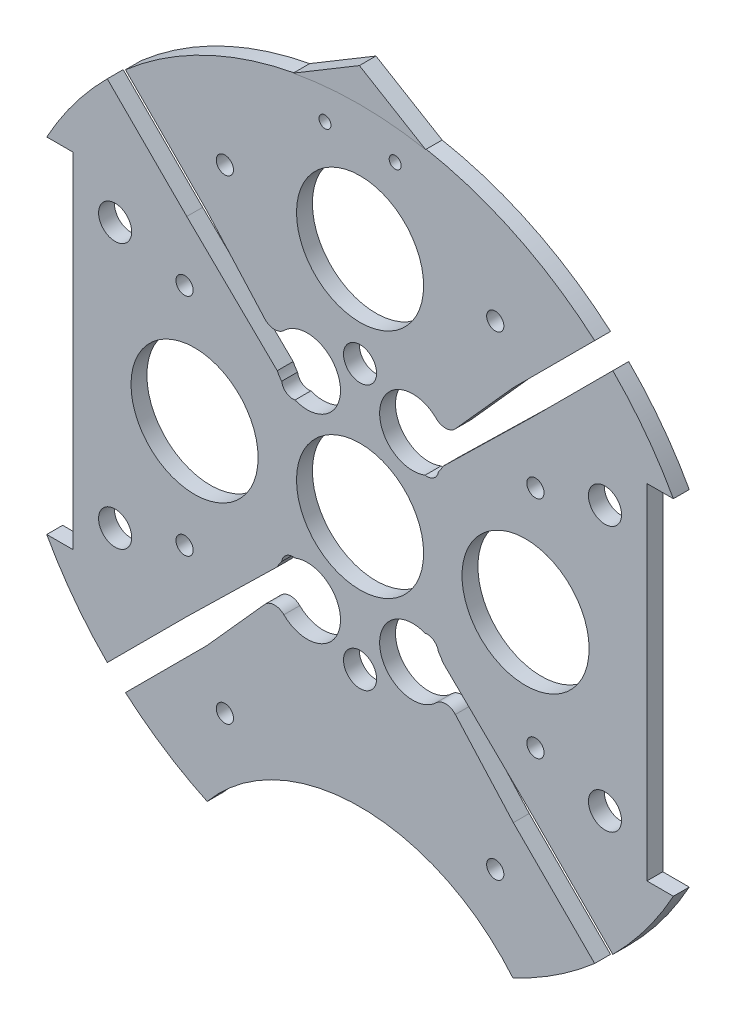
SolidWorks part; units mm, degrees
ref_plane "Front Plane" through (0, 0, 0) normal (0, 0, 1) x (1, 0, 0)
ref_plane "Top Plane" through (0, 0, 0) normal (0, 1, 0) x (1, 0, 0)
ref_plane "Right Plane" through (0, 0, 0) normal (1, 0, 0) x (0, 0, -1)
sketch "Sketch1" plane through (0, 0, 0) normal (0, 0, 1) x (1, 0, 0)
  line L0 (0, 0) -> (-82.1241, 0) construction
  line L1 (0, 0) -> (0, 95.6219) construction
  line L3 (-60.1074, 33.02) -> (-55.0274, 33.02)
  line L5 (-60.1074, -33.02) -> (-55.0274, -33.02)
  line L6 (-55.0274, 33.02) -> (-55.0274, -33.02)
  line L7 (60.1074, -33.02) -> (55.0274, -33.02)
  line L8 (60.1074, 33.02) -> (55.0274, 33.02)
  line L9 (55.0274, 33.02) -> (55.0274, -33.02)
  arc A0 (-60.1074, -33.02) -> (60.1074, -33.02) centre (0, 0) ccw
  circle A1 centre (-46.482, 10.795) radius 1.651 construction
  circle A2 centre (-21.082, 10.795) radius 1.651 construction
  circle A3 centre (-21.082, -10.795) radius 1.651 construction
  circle A4 centre (-46.482, -10.795) radius 1.651 construction
  circle A5 centre (46.482, -10.795) radius 1.651 construction
  circle A6 centre (21.082, -10.795) radius 1.651 construction
  circle A7 centre (21.082, 10.795) radius 1.651 construction
  circle A8 centre (46.482, 10.795) radius 1.651 construction
  arc A9 (60.1074, 33.02) -> (-60.1074, 33.02) centre (0, 0) ccw
  dimension "D2" = 3.302
  dimension "D3" = 3.302
  dimension "D4" = 25.4
  dimension "D5" = 10.795
  dimension "D10" = 46.482
  dimension "D12" = 10.795
  dimension "D6" = 66.04
  dimension "D7" = 5.08
  dimension "D8" = 68.58
  dimension "D9" = 68.58
  dimension "D11" = 33.02
extrude "Boss-Extrude2" add sketch "Sketch1" along normal blind 3.048
sketch "Sketch4" plane through (0, 0, 0) normal (0, 0, -1) x (-1, 0, 0)
  line L0 (0, 0) -> (0, -122.8047) construction
  line L1 (33.02, -67.2621) -> (-33.02, -67.2621)
  arc A0 (-60.1074, -33.02) -> (60.1074, -33.02) centre (0, 0) ccw construction
  circle A1 centre (0, -86.3121) radius 38.1
  dimension "D4" = 76.2
  dimension "D5" = 0
  dimension "D6" = 19.05
  dimension "D1" = 74.93
  dimension "D2" = 74.93
  dimension "D3" = 66.04
extrude "Cut-Extrude3" cut sketch "Sketch4" against normal through all
sketch "Sketch9" plane through (0, 0, 0) normal (0, 0, -1) x (-1, 0, 0)
  line L0 (12.7, 67.3938) -> (0, 75)
  line L1 (0, 75) -> (-12.7, 67.3938)
  arc A2 (12.7, 67.3938) -> (-12.7, 67.3938) centre (0, 0) ccw
extrude "Boss-Extrude3" add sketch "Sketch9" against normal blind 3.175
extrude "Cut-Extrude7" cut sketch "Sketch10" against normal through all
sketch "Sketch10" plane through (-31.3134, 132.559, 6.35) normal (0, 0, 1) x (0, 1, 0)
  line L0 (-132.559, -31.3134) -> (-245.9178, -31.3134) construction
  line L1 (-132.559, -31.3134) -> (-132.559, -129.4011) construction
  circle A0 centre (-180.819, -4.6434) radius 1.651
  circle A3 centre (-180.819, -57.9834) radius 1.651
  circle A4 centre (-84.299, -57.9834) radius 1.651
  circle A5 centre (-84.299, -4.6434) radius 1.651
extrude "Cut-Extrude8" cut sketch "Sketch11" against normal through all both and the other way through all
sketch "Sketch11" plane through (-31.3134, 132.614, 38.1) normal (0, 0, 1) x (0, 1, 0)
  line L0 (-132.614, -31.3134) -> (-132.614, 57.8454) construction
  line L1 (-132.614, -31.3134) -> (-222.516, -31.3134) construction
  circle A0 centre (-158.014, 14.4066) radius 3.175
  circle A1 centre (-173.254, -31.3134) radius 3.175
  circle A3 centre (-158.014, -77.0334) radius 3.175
  circle A4 centre (-107.214, -77.0334) radius 3.175
  circle A5 centre (-91.974, -31.3134) radius 3.175
  circle A6 centre (-107.214, 14.4066) radius 3.175
sketch "Sketch12" plane through (0, 0, 0) normal (0, 0, -1) x (-1, 0, 0)
  line L0 (0, -13.969) -> (0, 24.0636) construction
  circle A0 centre (6.731, 62.23) radius 1.143
  circle A1 centre (-6.731, 62.23) radius 1.143
  dimension "D1" = 2.286
  dimension "D2" = 62.23
  dimension "D3" = 6.731
extrude "Cut-Extrude9" cut sketch "Sketch12" against normal through all
extrude "Cut-Extrude12" cut sketch "Sketch15" against normal blind 75.692
sketch "Sketch15" plane through (30.092, 4.0835, -3.048) normal (0, 0, -1) x (-1, 0, 0)
  circle A0 centre (63.7572, 17.5065) radius 1.651
  circle A1 centre (63.7572, -25.6735) radius 1.651
  circle A2 centre (-3.5528, -25.6735) radius 1.651
  circle A3 centre (-3.5528, 17.5065) radius 1.651
extrude "Cut-Extrude14" cut sketch "Sketch17" against normal blind 97.79
sketch "Sketch17" plane through (30.092, 4.0835, -33.0835) normal (0, 0, -1) x (-1, 0, 0)
  line L0 (30.092, -29.4835) -> (30.092, 6.2385) construction
  circle A0 centre (4.1544, -49.7288) radius 1.651
  circle A4 centre (56.0296, -49.7288) radius 1.651
  circle A5 centre (4.1544, 41.3825) radius 1.651
  circle A9 centre (56.0296, 41.3825) radius 1.651
sketch "Sketch18" plane through (0, 0, 0) normal (0, 0, -1) x (-1, 0, 0)
  line L0 (0, 0) -> (0, -37.9941) construction
  circle A0 centre (31.75, 0) radius 12.192
  circle A1 centre (-31.75, 0) radius 12.192
  dimension "D1" = 24.384
  dimension "D2" = 31.75
extrude "Cut-Extrude15" cut sketch "Sketch18" against normal blind 35.56
extrude "Cut-Extrude16" cut sketch "Sketch19" against normal blind 48.768 and the other way blind 103.378
sketch "Sketch19" plane through (30.092, 4.0835, 3.048) normal (0, 0, -1) x (-1, 0, 0)
  line L0 (30.092, -4.0835) -> (148.6336, -4.0835) construction
  line L1 (30.092, -4.0835) -> (30.092, 90.452) construction
  circle A0 centre (-16.898, 21.3165) radius 3.175
  circle A1 centre (77.082, 21.3165) radius 3.175
  circle A2 centre (30.092, 21.3165) radius 3.175
  circle A4 centre (77.082, -29.4835) radius 3.175
  circle A5 centre (30.092, -29.4835) radius 3.175
  circle A6 centre (-16.898, -29.4835) radius 3.175
sketch "Sketch5" plane through (0, 0, 0) normal (0, 0, -1) x (-1, 0, 0)
  line L0 (45.1258, 51.861) -> (11.5228, 18.258) construction
  line L1 (-69.4248, 0) -> (69.4248, 0) construction
  line L2 (48.4934, -48.4934) -> (33.2448, -33.2448)
  line L3 (15.8876, 16.2964) -> (33.2448, 33.2448)
  line L4 (29.4103, -36.1455) -> (45.1258, -51.861)
  line L5 (45.1258, -51.861) -> (48.4934, -48.4934)
  line L6 (-15.2664, -15.2664) -> (-65.8076, -65.8076) construction
  line L7 (15.5824, -17.3784) -> (-2.7323, 0.9363) construction
  line L8 (16.1122, 21.3038) -> (29.4103, 36.1455)
  line L9 (-48.4934, 48.4934) -> (-6.6635, 6.6635) construction
  line L10 (-16.1122, 21.3038) -> (-29.4103, 36.1455)
  line L11 (48.4934, 48.4934) -> (15.2664, 15.2664) construction
  line L12 (-15.8876, 16.2964) -> (-33.2448, 33.2448)
  line L13 (0, 0) -> (46.9211, -12.5725) construction
  line L14 (29.4103, -36.1455) -> (16.1122, -21.3038)
  line L15 (-45.1258, 51.861) -> (-11.6404, 18.1832) construction
  line L16 (-45.1258, -51.861) -> (-13.0585, -19.7937) construction
  line L17 (45.1258, -51.861) -> (17.3018, -24.037) construction
  line L18 (0, 0) -> (-46.9211, -12.5725) construction
  line L19 (0, 0) -> (-0.898, -0.898) construction
  line L20 (33.2448, -33.2448) -> (15.8876, -16.2964)
  line L21 (4.9069, -1.3148) -> (-4.984, 8.5761) construction
  line L22 (-29.4103, -36.1455) -> (-16.1122, -21.3038)
  line L23 (-33.2448, -33.2448) -> (-15.8876, -16.2964)
  line L27 (-45.1258, -51.861) -> (-48.4934, -48.4934)
  line L28 (-29.4103, -36.1455) -> (-45.1258, -51.861)
  line L30 (0, 58.5122) -> (0, -56.1975) construction
  line L31 (-48.4934, -48.4934) -> (-33.2448, -33.2448)
  line L34 (-48.4934, 48.4934) -> (-33.2448, 33.2448)
  line L36 (-29.4103, 36.1455) -> (-45.1258, 51.861)
  line L37 (-45.1258, 51.861) -> (-48.4934, 48.4934)
  line L43 (15.2664, -15.2664) -> (65.8076, -65.8076) construction
  line L47 (0, 6.7352) -> (-14.4605, -7.7253) construction
  line L53 (45.1258, 51.861) -> (48.4934, 48.4934)
  line L54 (29.4103, 36.1455) -> (45.1258, 51.861)
  line L56 (48.4934, 48.4934) -> (33.2448, 33.2448)
  circle A0 centre (0, 0) radius 21.59 construction
  arc A1 (29.3285, -61.9924) -> (60.1074, -33.02) centre (0, 0) ccw construction
  arc A2 (12.4846, -13.1281) -> (15.0363, -14.9737) centre (12.8656, -15.2882) cw
  arc A3 (15.0363, 14.9737) -> (12.4846, 13.1281) centre (12.8656, 15.2882) cw
  arc A4 (-12.4846, 13.1281) -> (-15.0363, 14.9737) centre (-12.8656, 15.2882) cw
  arc A5 (-12.4846, -13.1281) -> (-15.0363, -14.9737) centre (-12.8656, -15.2882) ccw
  arc A6 (15.0363, 14.9737) -> (15.8876, 16.2964) centre (10.1352, 19.0632) ccw
  arc A7 (-15.0363, 14.9737) -> (-15.8876, 16.2964) centre (-10.1352, 19.0632) cw
  arc A8 (-15.0363, -14.9737) -> (-15.8876, -16.2964) centre (-10.1352, -19.0632) ccw
  arc A9 (15.0363, -14.9737) -> (15.8876, -16.2964) centre (10.1352, -19.0632) cw
  arc A10 (16.1122, 21.3038) -> (12.4846, 13.1281) centre (10.1352, 19.0632) ccw
  arc A11 (-16.1122, 21.3038) -> (-12.4846, 13.1281) centre (-10.1352, 19.0632) cw
  arc A12 (16.1122, -21.3038) -> (12.4846, -13.1281) centre (10.1352, -19.0632) cw
  arc A13 (-16.1122, -21.3038) -> (-12.4846, -13.1281) centre (-10.1352, -19.0632) ccw
  circle A14 centre (0, 0) radius 12.192
  circle A15 centre (0, 44.45) radius 12.192
  dimension "D7" = 44.45
  dimension "D6" = 43.18
  dimension "D5" = 24.384
  dimension "D1" = 12.7663
  dimension "D4" = 24.384
  dimension "D2" = 4.7625
  dimension "D3" = 22.225
  dimension "D9" = 15
extrude "Cut-Extrude6" cut sketch "Sketch5" against normal through all
fillet "Fillet1" radius 2.54 4 edges at (-16.1122, -21.3038, 1.524) (16.1122, -21.3038, 1.524) (16.1122, 21.3038, 1.524) (-16.1122, 21.3038, 1.524)
